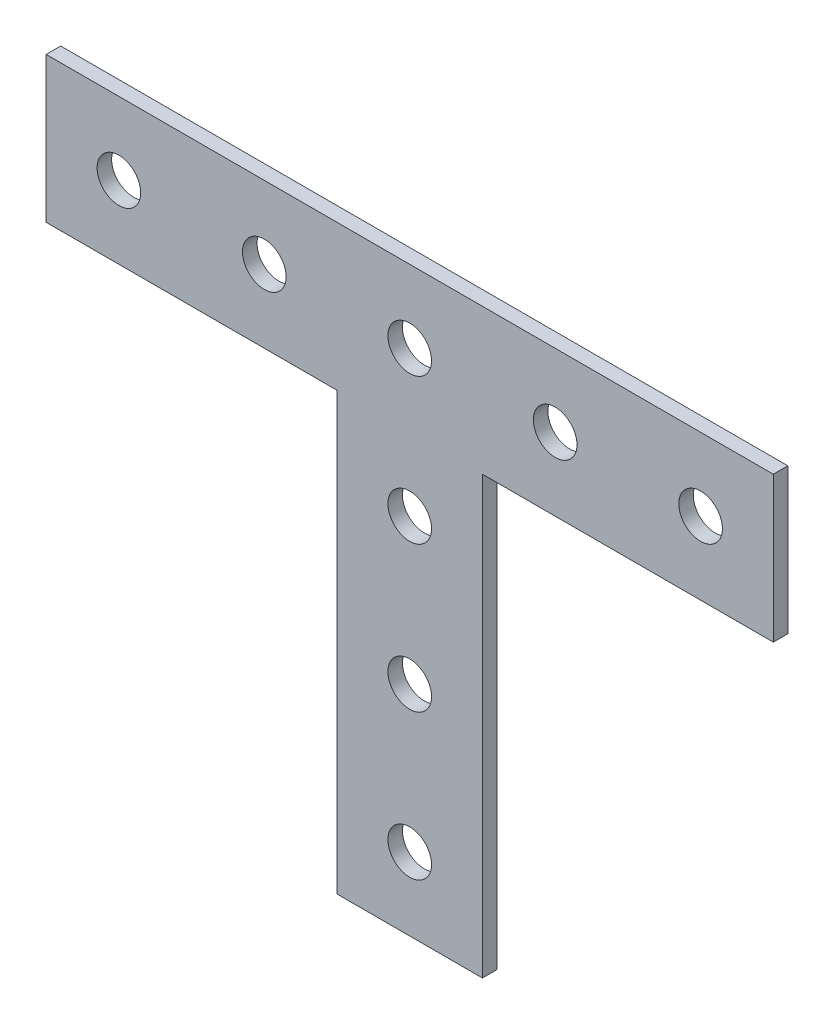
SolidWorks part; units mm, degrees
ref_plane "Front Plane" through (0, 0, 0) normal (0, 0, 1) x (1, 0, 0)
ref_plane "Top Plane" through (0, 0, 0) normal (0, 1, 0) x (1, 0, 0)
ref_plane "Right Plane" through (0, 0, 0) normal (1, 0, 0) x (0, 0, -1)
sketch "Esquisse1" plane through (0, 0, 0) normal (0, 0, 1) x (1, 0, 0)
  line L0 (-25, 10) -> (25, 10)
  line L1 (25, 10) -> (25, 0)
  line L2 (25, 0) -> (5, 0)
  line L3 (5, 0) -> (5, -30)
  line L4 (5, -30) -> (-5, -30)
  line L5 (-5, -30) -> (-5, 0)
  line L6 (-5, 0) -> (-25, 0)
  line L7 (-25, 0) -> (-25, 10)
  point P9 (0, -30)
  point P10 (0, 10)
  point P11 (24.9712, 0)
  dimension "D1" = 50
  dimension "D2" = 40
  dimension "D3" = 10
extrude "Boss.-Extru.1" add sketch "Esquisse1" along normal blind 1
sketch "Esquisse2" plane through (0, 0, 1) normal (0, 0, 1) x (1, 0, 0)
  line L0 (-25, 10) -> (-25, 0) construction
  circle A0 centre (0, 5) radius 1.5
  point P2 (0, 0)
  point P3 (0, 0)
  point P8 (-25, 5)
  dimension "D1" = 3
extrude "Enlèv. mat.-Extru.1" cut sketch "Esquisse2" against normal through all
pattern_linear "Répétition linéaire1" count 3 spacing 10 along (-1, 0, 0) of "Enlèv. mat.-Extru.1"
pattern_linear "Répétition linéaire2" count 3 spacing 10 along (1, 0, 0) of "Enlèv. mat.-Extru.1"
pattern_linear "Répétition linéaire3" count 4 spacing 10 along (0, -1, 0) of "Enlèv. mat.-Extru.1"
